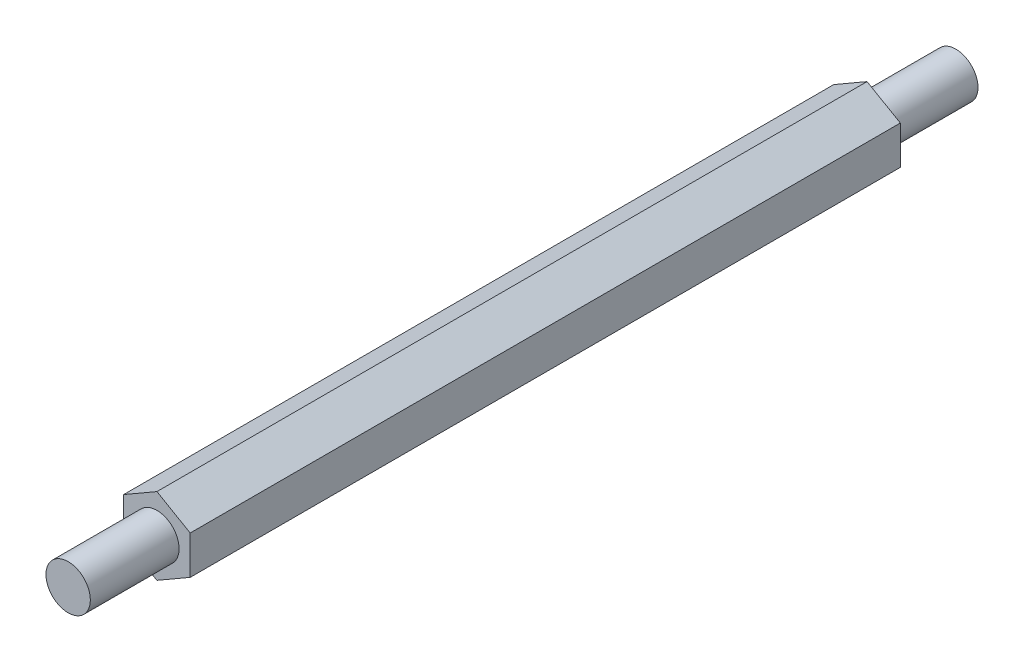
SolidWorks part; units mm, degrees
ref_plane "Front Plane" through (0, 0, 0) normal (0, 0, 1) x (1, 0, 0)
ref_plane "Top Plane" through (0, 0, 0) normal (0, 1, 0) x (1, 0, 0)
ref_plane "Right Plane" through (0, 0, 0) normal (1, 0, 0) x (0, 0, -1)
sketch "Sketch1" plane through (0, 0, 0) normal (0, 0, 1) x (1, 0, 0)
  line L1 (0, 10.9985) -> (-9.525, 5.4993)
  line L2 (-9.525, 5.4993) -> (-9.525, -5.4993)
  line L3 (-9.525, -5.4993) -> (0, -10.9985)
  line L4 (0, -10.9985) -> (9.525, -5.4993)
  line L5 (9.525, -5.4993) -> (9.525, 5.4993)
  line L6 (9.525, 5.4993) -> (0, 10.9985)
  circle A0 centre (0, 0) radius 9.525 construction
  dimension "D1" = 19.05
extrude "Boss-Extrude1" add sketch "Sketch1" along normal mid plane 203.2
sketch "Sketch2" plane through (0, 0, 0) normal (0, 0, 1) x (1, 0, 0)
  circle A0 centre (0, 0) radius 6.35
  dimension "D1" = 12.7
extrude "Boss-Extrude2" add sketch "Sketch2" along normal offset from surface 25.4 and the other way offset from surface (127 mm away) 25.4 up to face at (0, 0, 101.6) offset beyond the face yes other way up to face at (0, 0, -101.6)
